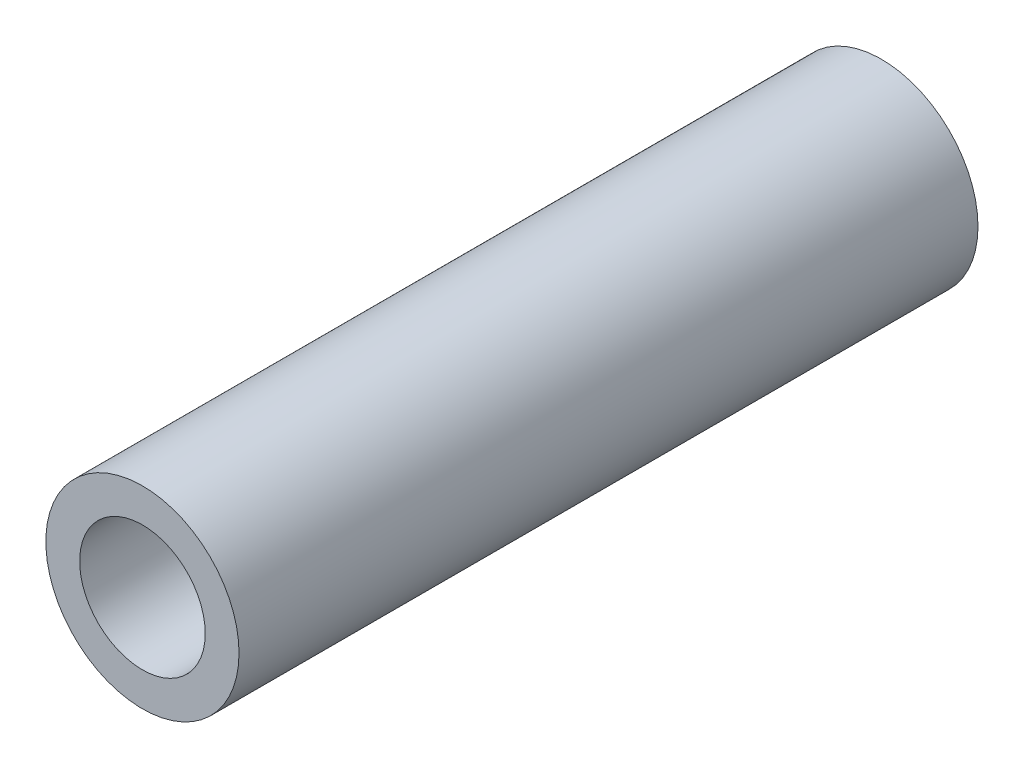
SolidWorks part; units mm, degrees
ref_plane "Front Plane" through (0, 0, 0) normal (0, 0, 1) x (1, 0, 0)
ref_plane "Top Plane" through (0, 0, 0) normal (0, 1, 0) x (1, 0, 0)
ref_plane "Right Plane" through (0, 0, 0) normal (1, 0, 0) x (0, 0, -1)
sketch "Sketch1" plane through (0, 0, 0) normal (0, 0, 1) x (1, 0, 0)
  circle A0 centre (0, 0) radius 2
  dimension "D1" = 4
extrude "Boss-Extrude1" add sketch "Sketch1" against normal blind 15.3
sketch "Sketch2" plane through (0, 0, 0) normal (0, 0, 1) x (1, 0, 0)
  circle A0 centre (0, 0) radius 1.3
  dimension "D1" = 2.6
extrude "Cut-Extrude1" cut sketch "Sketch2" against normal through all
